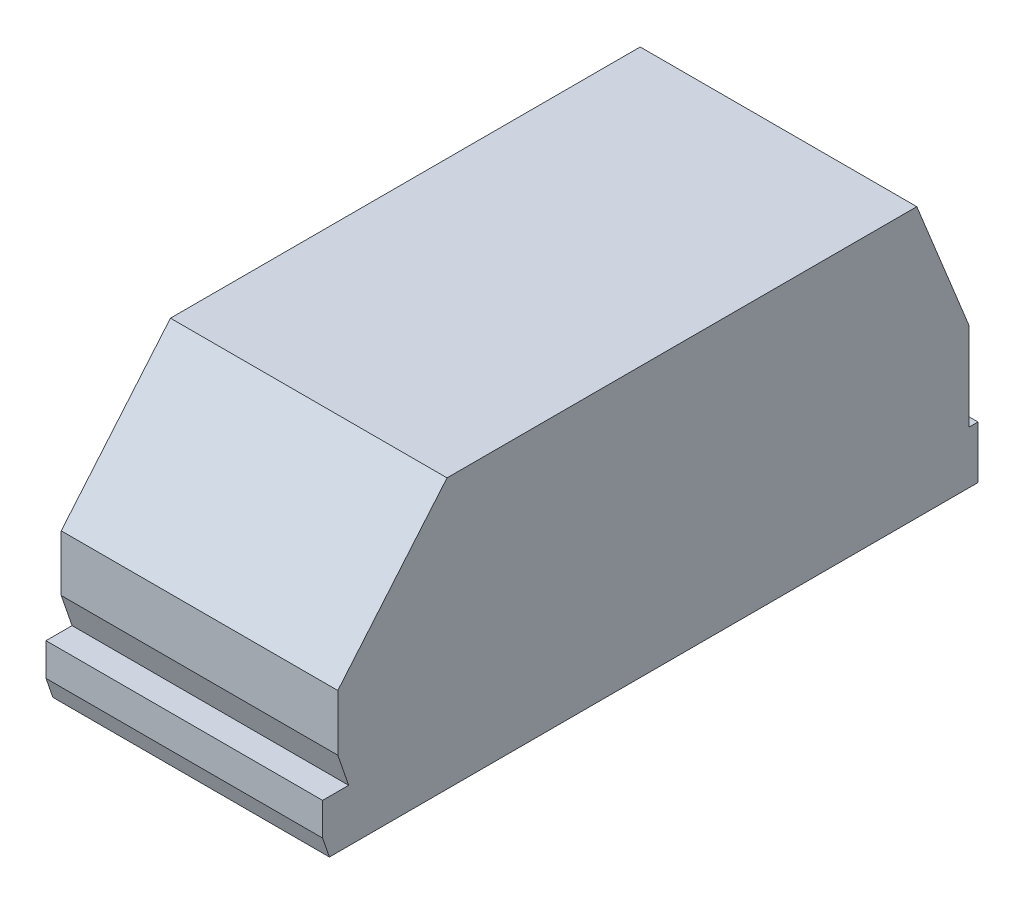
SolidWorks part; units mm, degrees
ref_plane "Front Plane" through (0, 0, 0) normal (0, 0, 1) x (1, 0, 0)
ref_plane "Top Plane" through (0, 0, 0) normal (0, 1, 0) x (1, 0, 0)
ref_plane "Right Plane" through (0, 0, 0) normal (1, 0, 0) x (0, 0, -1)
sketch "Sketch6" plane through (0, 0, 0) normal (1, 0, 0) x (0, 0, -1)
  line L0 (-68.65, 0.8497) -> (58.0664, 0.8497) construction
  line L1 (-85.7428, -14.3255) -> (-88.8417, -5.3255)
  line L2 (-88.8417, -5.3255) -> (-88.8417, 10.6745)
  line L3 (-88.8417, 10.6745) -> (-57.6495, 47.6745)
  line L4 (-57.6495, 47.6745) -> (76.5266, 47.6745)
  line L5 (76.5266, 47.6745) -> (88.4256, 18.2923)
  line L6 (88.4256, 18.2923) -> (91.5107, 10.6745)
  line L9 (91.5107, -14.3255) -> (94.0107, -14.3255)
  line L10 (94.0107, -14.3255) -> (94.0107, -29.3255)
  line L11 (94.0107, -29.3255) -> (-80.4455, -29.3255)
  line L12 (-80.4455, -29.3255) -> (-91.2359, -29.3255)
  line L13 (-91.2359, -29.3255) -> (-93.1893, -23.6524)
  line L14 (-93.1893, -23.6524) -> (-93.1893, -14.3255)
  line L15 (-93.1893, -14.3255) -> (-85.7428, -14.3255)
  line L16 (91.5107, 10.6745) -> (91.5107, -14.3255)
  line L17 (-88.8417, 10.6745) -> (91.5107, 10.6745) construction
  dimension "D1" = 187.2
  dimension "D2" = 77
  dimension "D3" = 37
  dimension "D4" = 15
  dimension "D5" = 161
  dimension "D6" = 6
  dimension "D7" = 37
  dimension "D8" = 25
  dimension "D9" = 15
  dimension "D10" = 2.5
  dimension "D11" = 16
extrude "Boss-Extrude2" add sketch "Sketch6" along normal mid plane 79
ref_plane "Plane2" through (0, 11, 0) normal (0, 1, 0) x (1, 0, 0)
sketch "Sketch7" plane through (0, 11, 0) normal (0, 1, 0) x (1, 0, 0)
  line L0 (-39.5, -86.8417) -> (39.5, -86.8417) construction
  line L3 (-39.5, -57.6495) -> (-39.5, -88.8417) construction
  line L4 (39.5, -57.6495) -> (39.5, -88.8417) construction
  line L5 (39.5, -88.8417) -> (-39.5, -88.8417) construction
  line L6 (39.5, -88.8417) -> (22.8491, -88.8417)
  line L7 (-39.5, -86.8417) -> (-39.5, -88.8417)
  line L8 (39.5, -86.8417) -> (39.5, -88.8417)
  line L9 (-22.8491, -88.8417) -> (-39.5, -88.8417)
  arc A0 (-39.5, -86.8417) -> (-22.8491, -88.8417) centre (0, 171.7) ccw
  arc A1 (22.8491, -88.8417) -> (39.5, -86.8417) centre (0, 171.7) ccw
  dimension "D1" = 2
